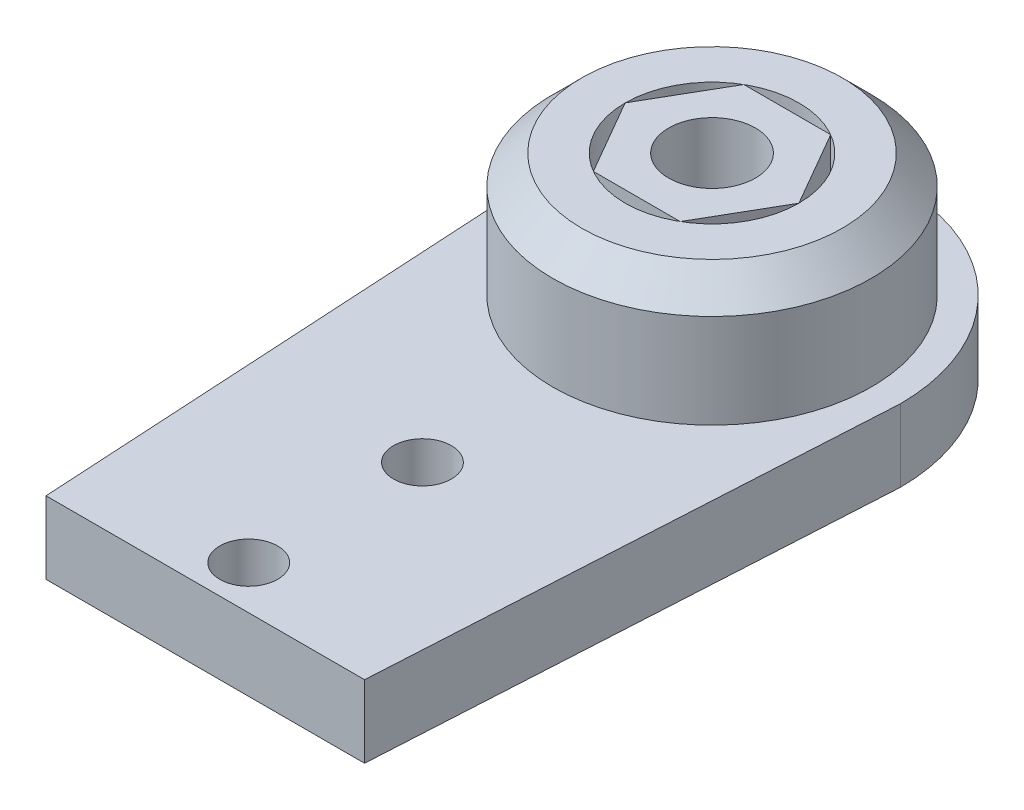
SolidWorks part; units mm, degrees
ref_plane "Front Plane" through (0, 0, 0) normal (0, 0, 1) x (1, 0, 0)
ref_plane "Top Plane" through (0, 0, 0) normal (0, 1, 0) x (1, 0, 0)
ref_plane "Right Plane" through (0, 0, 0) normal (1, 0, 0) x (0, 0, -1)
sketch "Sketch1" plane through (0, 0, 0) normal (0, 1, 0) x (1, 0, 0)
  line L0 (-6.5, 0) -> (-5.5, -17.5)
  line L1 (-5.5, -17.5) -> (5.5, -17.5)
  line L2 (5.5, -17.5) -> (6.5, 0)
  arc A0 (6.4577, -0.7404) -> (-6.4577, -0.7404) centre (0, 0) ccw
  circle A1 centre (0, -10) radius 1
  circle A2 centre (0, -16) radius 1
  dimension "D1" = 13
  dimension "D2" = 24
  dimension "D5" = 2
  dimension "D6" = 2
  dimension "D7" = 3.5
  dimension "D3" = 11
  dimension "D4" = 13
  dimension "D8" = 6
extrude "Boss-Extrude1" add sketch "Sketch1" along normal blind 2.5 contours L2 A0 L0 L1 A2 A1
sketch "Sketch2" plane through (0, 2.5, 0) normal (0, 1, 0) x (1, 0, 0)
  circle A0 centre (0, 0) radius 5.5
  circle A1 centre (0, 0) radius 3
  dimension "D1" = 11
  dimension "D2" = 6
extrude "Boss-Extrude3" add sketch "Sketch2" along normal blind 4.25
sketch "Sketch4" plane through (0, 2.5, 0) normal (0, 1, 0) x (1, 0, 0)
  circle A0 centre (0, 0) radius 3
extrude "Cut-Extrude1" cut sketch "Sketch4" against normal up to next
chamfer "Chamfer1" distance 1 angle 45 1 edges at (0, 6.75, 5.5)
sketch "Sketch5" plane through (0, 6.75, 0) normal (0, 1, 0) x (1, 0, 0)
  line L1 (3, 0) -> (1.5, 2.5981)
  line L2 (1.5, 2.5981) -> (-1.5, 2.5981)
  line L3 (-1.5, 2.5981) -> (-3, 0)
  line L4 (-3, 0) -> (-1.5, -2.5981)
  line L5 (-1.5, -2.5981) -> (1.5, -2.5981)
  line L6 (1.5, -2.5981) -> (3, 0)
  circle A0 centre (0, 0) radius 2.5981 construction
  circle A1 centre (0, 0) radius 1.5
  circle A2 centre (0, 0) radius 3 construction
  dimension "D1" = 3
extrude "Boss-Extrude4" add sketch "Sketch5" against normal blind 2.5 separate body
